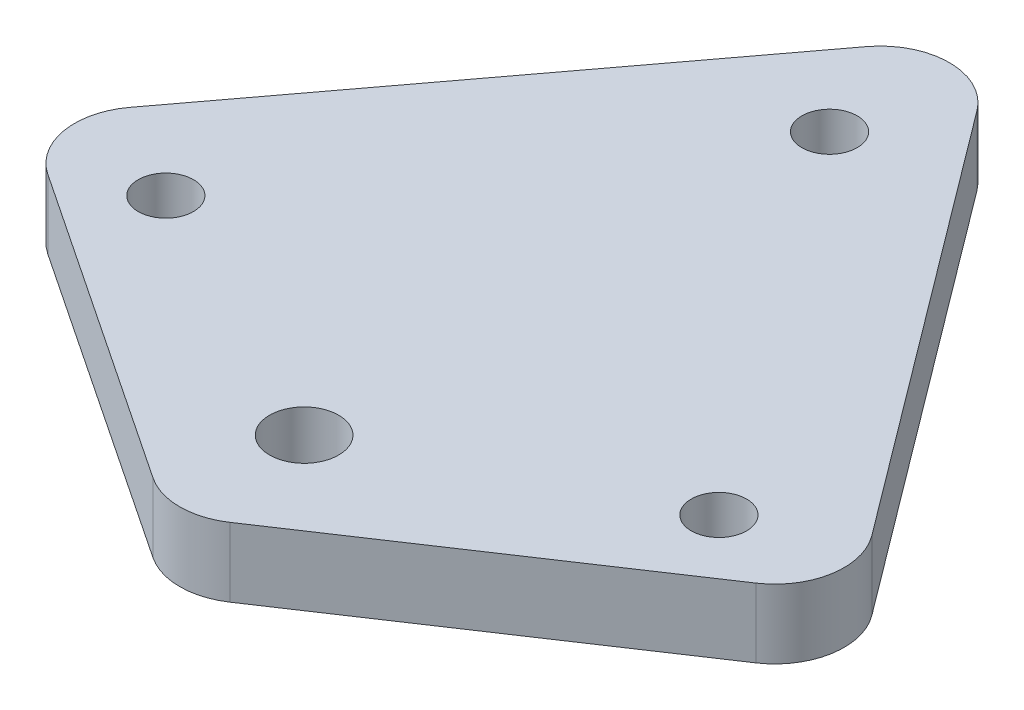
SolidWorks part; units mm, degrees
ref_plane "Front Plane" through (0, 0, 0) normal (0, 0, 1) x (1, 0, 0)
ref_plane "Top Plane" through (0, 0, 0) normal (0, 1, 0) x (1, 0, 0)
ref_plane "Right Plane" through (0, 0, 0) normal (1, 0, 0) x (0, 0, -1)
sketch "Sketch2" plane through (0, 0, 0) normal (0, 1, 0) x (1, 0, 0)
  line L0 (0, 63.5) -> (0, -12.7) construction
  line L1 (0, 63.5) -> (-38.1, 12.7)
  line L2 (0, 63.5) -> (38.1, 12.7)
  line L3 (38.1, 12.7) -> (-38.1, 12.7) construction
  line L5 (-38.1, 12.7) -> (0, -12.7)
  line L8 (38.1, 12.7) -> (0, -12.7)
  circle A0 centre (0, 0) radius 3.175
  circle A1 centre (-25.4, 12.7) radius 2.54
  circle A2 centre (0, 48.26) radius 2.54
  circle A3 centre (25.4, 12.7) radius 2.54
  dimension "D4" = 12.7
  dimension "D7" = 76.2
  dimension "D3" = 6.35
  dimension "D1" = 5.08
  dimension "D5" = 12.7
  dimension "D2" = 12.7
  dimension "D6" = 15.24
  dimension "D8" = 76.2
extrude "Boss-Extrude2" add sketch "Sketch2" along normal blind 6.35
fillet "Fillet3" radius 6.35 4 edges at (0, 3.175, -63.5) (38.1, 3.175, -12.7) (-38.1, 3.175, -12.7) (0, 3.175, 12.7)
sketch "Sketch3" plane through (0, 6.35, 0) normal (0, 1, 0) x (1, 0, 0)
  line L0 (-25.4, 12.7) -> (25.4, 12.7) construction
